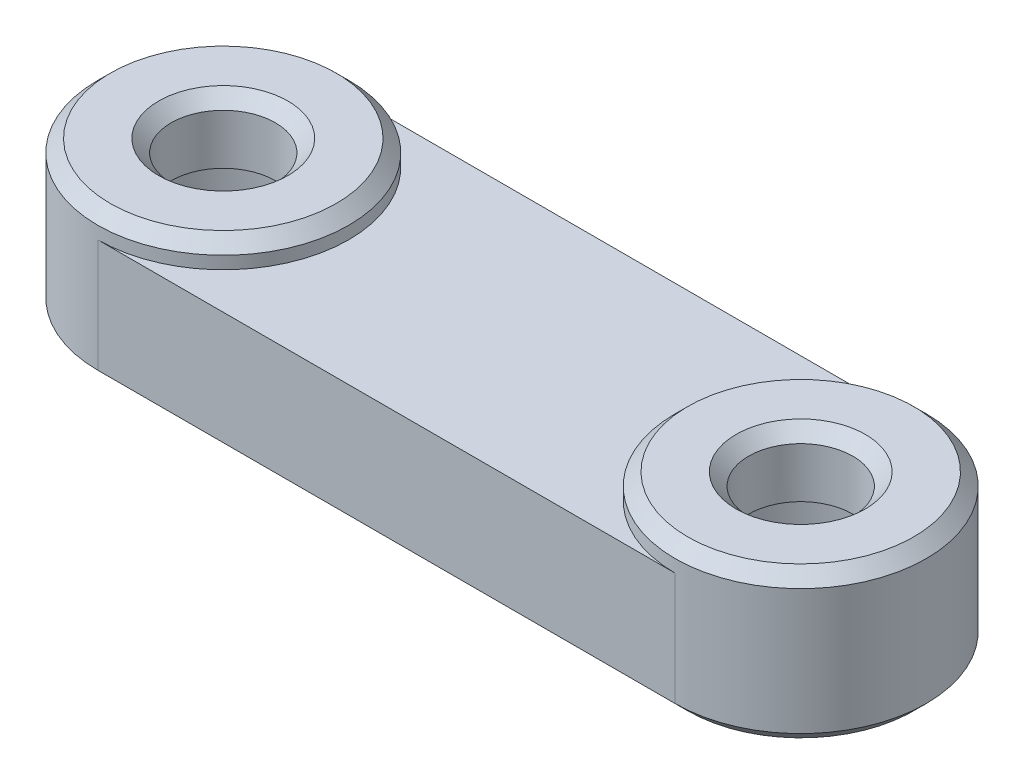
SolidWorks part; units mm, degrees
ref_plane "Front Plane" through (0, 0, 0) normal (0, 0, 1) x (1, 0, 0)
ref_plane "Top Plane" through (0, 0, 0) normal (0, 1, 0) x (1, 0, 0)
ref_plane "Right Plane" through (0, 0, 0) normal (1, 0, 0) x (0, 0, -1)
sketch "Sketch2" plane through (0, 0, 0) normal (0, 1, 0) x (1, 0, 0)
  line L0 (0, 0) -> (23, 0) construction
  line L1 (0, 5) -> (23, 5)
  line L2 (0, -5) -> (23, -5)
  arc A0 (0, 5) -> (0, -5) centre (0, 0) ccw
  arc A1 (23, -5) -> (23, 5) centre (23, 0) ccw
  point P3 (11.5, 0)
  dimension "D1" = 23
  dimension "D2" = 10
extrude "Boss-Extrude1" add sketch "Sketch2" along normal blind 6
sketch "Sketch3" plane through (0, 0, 0) normal (0, 0, 1) x (1, 0, 0)
  line L0 (0, 0) -> (0, 11.9265) construction
  line L1 (0, 0) -> (-3.75, 0)
  line L2 (-5, 0) -> (0, 0) construction
  line L3 (-3.75, 0) -> (-3.75, 3.5)
  line L4 (-3.75, 3.5) -> (-2.075, 3.5)
  line L5 (-2.075, 3.5) -> (-2.075, 6)
  line L6 (0, 6) -> (-5, 6) construction
  line L7 (-2.075, 6) -> (0, 6)
  line L8 (0, 0) -> (0, 6)
  point P3 (-3.75, 1.75)
  dimension "D1" = 4.15
  dimension "D2" = 7.5
  dimension "D3" = 3.5
revolve "Cut-Revolve1" cut sketch "Sketch3" angle 360 about L8
sketch "Sketch4" plane through (0, 0, 0) normal (0, 0, 1) x (1, 0, 0)
  line L0 (23, 0) -> (23, 11.7791) construction
  line L1 (23, 0) -> (19.25, 0)
  line L2 (0, 0) -> (23, 0) construction
  line L3 (19.25, 0) -> (19.25, 3.5)
  line L4 (19.25, 3.5) -> (20.925, 3.5)
  line L5 (20.925, 3.5) -> (20.925, 6)
  line L6 (0, 6) -> (23, 6) construction
  line L7 (20.925, 6) -> (23, 6)
  line L8 (23, 0) -> (23, 6)
  dimension "D1" = 4.15
  dimension "D2" = 7.5
  dimension "D3" = 3.5
revolve "Cut-Revolve2" cut sketch "Sketch4" angle 360 about L8
sketch "Sketch5" plane through (0, 6, 0) normal (0, 1, 0) x (1, 0, 0)
  line L1 (-15.0757, 11.122) -> (35.7053, 11.122)
  line L2 (-15.0757, 11.122) -> (-15.0757, -10.963)
  line L3 (-15.0757, -10.963) -> (35.7053, -10.963)
  line L4 (35.7053, 11.122) -> (35.7053, -10.963)
  circle A0 centre (0, 0) radius 5
  circle A1 centre (23, 0) radius 5
  dimension "D1" = 10
  dimension "D2" = 10
extrude "Cut-Extrude1" cut sketch "Sketch5" against normal blind 1
chamfer "Chamfer2" distance 0.5 angle 45 8 edges at (23, 6, 5) (23, 6, -2.075) (0, 6, 5) (0, 6, -2.075) (11.5, 0, -5) (-5, 0, 0) (28, 0, 0) (11.5, 0, 5)
